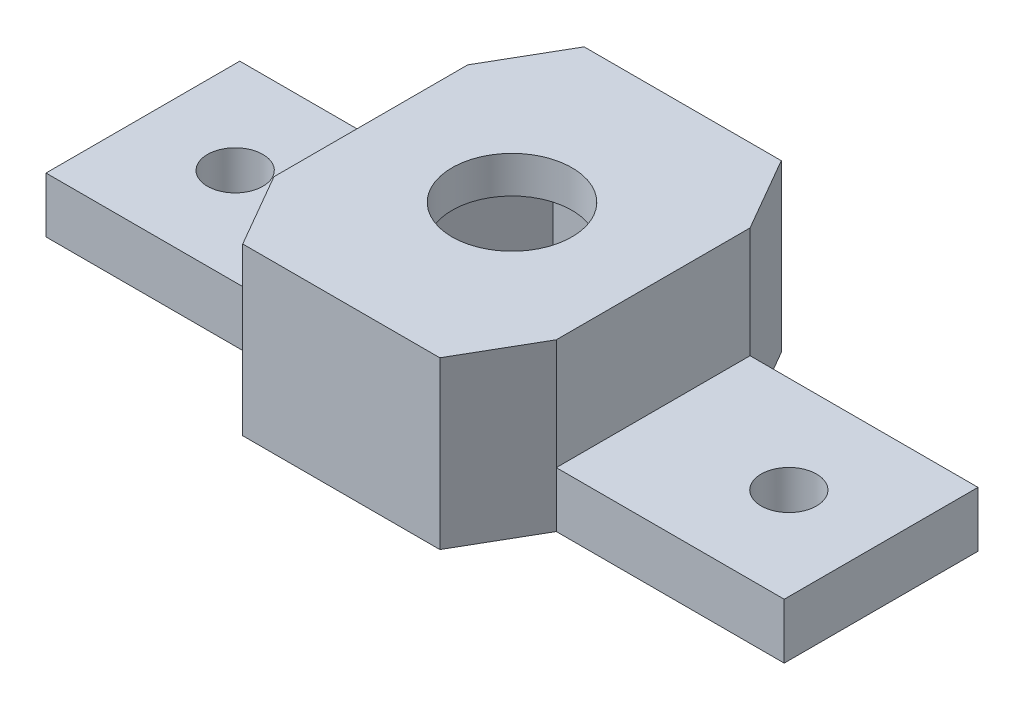
SolidWorks part; units mm, degrees
ref_plane "Plan de face" through (0, 0, 0) normal (0, 0, 1) x (1, 0, 0)
ref_plane "Plan de dessus" through (0, 0, 0) normal (0, 1, 0) x (1, 0, 0)
ref_plane "Plan de droite" through (0, 0, 0) normal (1, 0, 0) x (0, 0, -1)
sketch "Esquisse1" plane through (0, 0, 0) normal (0, 1, 0) x (1, 0, 0)
  line L0 (5.3405, 9.25) -> (-5.3405, 9.25)
  line L1 (6.0622, 0) -> (3.0311, 5.25)
  line L2 (3.0311, 5.25) -> (-3.0311, 5.25)
  line L3 (-3.0311, 5.25) -> (-6.0622, 0)
  line L4 (-6.0622, 0) -> (-3.0311, -5.25)
  line L5 (-3.0311, -5.25) -> (3.0311, -5.25)
  line L6 (3.0311, -5.25) -> (6.0622, 0)
  line L7 (-5.3405, 9.25) -> (-7.6499, 5.25)
  line L8 (-7.6499, -5.25) -> (-5.3405, -9.25)
  line L9 (-5.3405, -9.25) -> (5.3405, -9.25)
  line L10 (5.3405, -9.25) -> (7.6499, -5.25)
  line L11 (7.6499, 5.25) -> (5.3405, 9.25)
  line L12 (-7.6499, 5.25) -> (-20, 5.25)
  line L13 (-7.6499, 5.25) -> (7.6499, 5.25) construction
  line L14 (7.6499, 5.25) -> (7.6499, -5.25) construction
  line L15 (7.6499, -5.25) -> (-7.6499, -5.25) construction
  line L16 (-7.6499, -5.25) -> (-7.6499, 5.25) construction
  line L17 (-20, 5.25) -> (-20, -5.25)
  line L18 (-20, -5.25) -> (-7.6499, -5.25)
  line L19 (0, 9.25) -> (0, -9.25) construction
  line L20 (-5.3405, 9.25) -> (-10.681, 0) construction
  line L21 (-10.681, 0) -> (-5.3405, -9.25) construction
  line L22 (20, -5.25) -> (7.6499, -5.25)
  line L23 (20, 5.25) -> (20, -5.25)
  line L24 (7.6499, 5.25) -> (20, 5.25)
  line L25 (5.3405, -9.25) -> (10.681, 0) construction
  line L26 (10.681, 0) -> (5.3405, 9.25) construction
  line L27 (-20, 0) -> (20, 0) construction
  line L28 (20, 0) -> (-20, 0) construction
  circle A0 centre (0, 0) radius 5.25 construction
  circle A1 centre (-15, 0) radius 1.5
  circle A2 centre (15, 0) radius 1.5
  dimension "D1" = 10.5
  dimension "D4" = 3
  dimension "D5" = 15
  dimension "D2" = 4
  dimension "D3" = 20
extrude "Boss.-Extru.1" add sketch "Esquisse1" along normal blind 7
sketch "Esquisse2" plane through (0, 0, 5.25) normal (0, 0, 1) x (1, 0, 0)
  line L0 (-7.6499, 7) -> (-7.6499, 0) construction
  line L1 (-20, 7) -> (-7.6499, 7)
  line L2 (-20, 7) -> (-20, 3)
  line L3 (-20, 3) -> (-7.6499, 3)
  line L4 (-7.6499, 7) -> (-7.6499, 3)
  line L5 (-20, 0) -> (-7.6499, 0) construction
  line L6 (0, 0) -> (0, 7) construction
  line L7 (-5.3405, 7) -> (5.3405, 7) construction
  line L8 (7.6499, 7) -> (7.6499, 3)
  line L9 (20, 3) -> (7.6499, 3)
  line L10 (20, 7) -> (20, 3)
  line L11 (20, 7) -> (7.6499, 7)
  dimension "D1" = 3
extrude "Enlèv. mat.-Extru.1" cut sketch "Esquisse2" against normal up to next
sketch "Esquisse3" plane through (0, 7, 0) normal (0, 1, 0) x (1, 0, 0)
  line L0 (-7.6499, -5.25) -> (-7.6499, 5.25)
  line L1 (-7.6499, 5.25) -> (-5.3405, 9.25)
  line L2 (-5.3405, 9.25) -> (5.3405, 9.25)
  line L3 (5.3405, 9.25) -> (7.6499, 5.25)
  line L4 (7.6499, 5.25) -> (7.6499, -5.25)
  line L5 (7.6499, -5.25) -> (5.3405, -9.25)
  line L6 (5.3405, -9.25) -> (-5.3405, -9.25)
  line L7 (-5.3405, -9.25) -> (-7.6499, -5.25)
  circle A0 centre (0, 0) radius 3.25
  dimension "D1" = 6.5
extrude "Boss.-Extru.2" add sketch "Esquisse3" along normal blind 2
